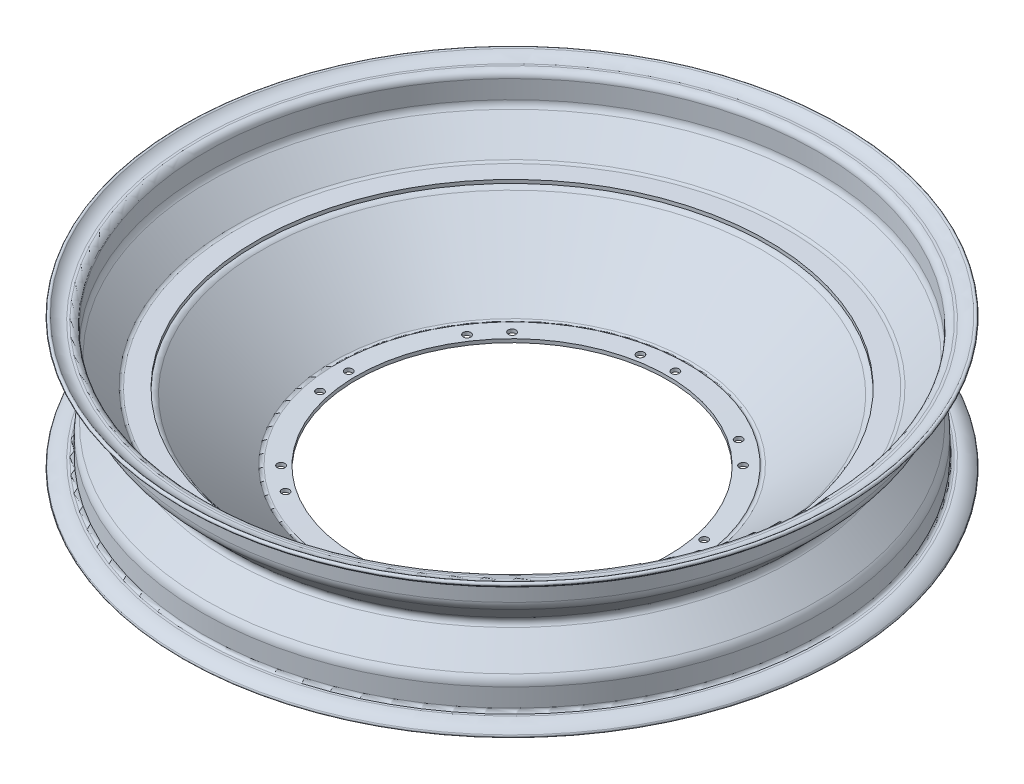
SolidWorks part; units mm, degrees
material "6061-T6 (SS)"
ref_plane "Front Plane" through (0, 0, 0) normal (0, 0, 1) x (1, 0, 0)
ref_plane "Top Plane" through (0, 0, 0) normal (0, 1, 0) x (1, 0, 0)
ref_plane "Right Plane" through (0, 0, 0) normal (1, 0, 0) x (0, 0, -1)
sketch "Sketch3" plane through (0, 0, 0) normal (0, 0, 1) x (1, 0, 0)
  line L0 (-167.2903, -3.117) -> (0, 0) construction
  line L2 (-206.3572, 37.168) -> (-204.8572, 37.168)
  line L3 (-200.5712, 32.882) -> (-200.5712, 20.882)
  line L4 (-198.7835, 16.7306) -> (-182.0435, -0.009)
  line L5 (-180.0484, -0.831) -> (-167.2903, -0.831)
  line L6 (-198.8174, -22.999) -> (-182.051, -6.2325)
  line L7 (-200.5712, -39.118) -> (-200.5712, -27.118)
  line L8 (-206.3572, -43.404) -> (-204.8572, -43.404)
  line L9 (-187.8252, -3.117) -> (-167.2903, -3.117) construction
  line L11 (-165.3527, -6.1688) -> (-118.8975, -46.2519)
  line L12 (-114.3834, -46.9352) -> (-102, -47.2925)
  line L13 (-114.3834, -46.9352) -> (-104.286, -47.2266) construction
  line L14 (-180.0484, -5.403) -> (-167.2903, -5.403)
  line L15 (-167.2903, -3.117) -> (-167.2903, 0) construction
  line L17 (-102, -45.0056) -> (-102, -48.1245) construction
  line L18 (-200.4193, -21.368) -> (-183.6674, -4.6161) construction
  line L19 (-202.8572, -39.118) -> (-202.8572, -27.118)
  line L21 (-200.4193, -21.368) -> (-184.9968, -5.9455)
  line L24 (-202.8572, 32.882) -> (-202.8572, 20.882)
  line L26 (-206.3572, 34.882) -> (-204.8572, 34.882)
  line L27 (-200.3793, 15.0935) -> (-184.9968, -0.2886)
  line L29 (-167.2903, -3.117) -> (-167.2903, -0.831)
  line L33 (-163.8292, -4.464) -> (-117.4041, -44.5211)
  line L34 (-114.9323, -44.6324) -> (-102, -45.0056)
  line L35 (-102, -45.0056) -> (-102, -47.2925)
  line L36 (-200.3793, 15.0935) -> (-183.6574, -1.628) construction
  line L39 (-206.3572, -41.118) -> (-204.8572, -41.118)
  line L41 (0, 240.889) -> (0, -99.5724) construction
  line L44 (-178.7196, -0.4999) -> (-178.7215, -5.7331) construction
  line L45 (-169.5763, -6.5618) -> (-169.5763, 0) construction
  line L46 (-104.286, -47.2266) -> (-104.286, -48.1245) construction
  line L47 (-181.0065, -3.0266) -> (-181.0066, -3.2075) construction
  arc A0 (-213.9267, 40.5243) -> (-206.3572, 37.168) centre (-206.3572, 47.382) ccw
  arc A1 (-200.5712, 32.882) -> (-204.8572, 37.168) centre (-204.8572, 32.882) ccw
  arc A2 (-200.5712, 20.882) -> (-198.7835, 16.7306) centre (-194.8572, 20.882) ccw
  arc A3 (-182.0435, -0.009) -> (-180.0484, -0.831) centre (-180.0484, 2.001) ccw
  arc A4 (-180.0484, -5.403) -> (-182.051, -6.2325) centre (-180.0484, -8.2351) ccw
  arc A6 (-198.8174, -22.999) -> (-200.5712, -27.118) centre (-194.8572, -27.118) ccw
  arc A7 (-204.8572, -43.404) -> (-200.5712, -39.118) centre (-204.8572, -39.118) ccw
  arc A8 (-206.3572, -43.404) -> (-213.9267, -46.7603) centre (-206.3572, -53.618) ccw
  arc A9 (-165.3527, -6.1688) -> (-167.2903, -5.403) centre (-167.2903, -8.2374) ccw
  arc A10 (-118.8975, -46.2519) -> (-114.3834, -46.9352) centre (-116.0975, -43.0067) ccw
  arc A11 (-182.0435, -0.009) -> (-178.7196, -0.4999) centre (-180.0484, 2.001) ccw construction
  arc A12 (-165.3527, -6.1688) -> (-169.5763, -6.5618) centre (-167.2903, -8.2374) ccw construction
  arc A13 (-178.7215, -5.7331) -> (-182.051, -6.2325) centre (-180.0484, -8.2351) ccw construction
  arc A14 (-213.9267, 40.5243) -> (-215.6209, 38.9895) centre (-214.7738, 39.7569) ccw
  arc A15 (-213.9267, -46.7603) -> (-215.6209, -45.2255) centre (-214.7738, -45.9929) cw
  arc A17 (-183.6574, -1.628) -> (-181.0065, -3.0266) centre (-180.0484, 2.001) ccw construction
  arc A18 (-204.8572, -41.118) -> (-202.8572, -39.118) centre (-204.8572, -39.118) ccw
  arc A20 (-200.4193, -21.368) -> (-202.8572, -27.118) centre (-194.8572, -27.118) ccw
  arc A22 (-202.8572, 20.882) -> (-200.3793, 15.0935) centre (-194.8572, 20.882) ccw
  arc A24 (-202.8572, 32.882) -> (-204.8572, 34.882) centre (-204.8572, 32.882) ccw
  arc A28 (-215.6209, 38.9895) -> (-206.3572, 34.882) centre (-206.3572, 47.382) ccw
  arc A31 (-181.0066, -3.2075) -> (-183.6674, -4.6161) centre (-180.0484, -8.2351) ccw construction
  arc A33 (-163.8292, -4.464) -> (-167.2903, -3.117) centre (-167.2903, -8.2374) ccw
  arc A35 (-117.4041, -44.5211) -> (-114.9323, -44.6324) centre (-116.0975, -43.0067) ccw
  arc A36 (-184.9968, -5.9455) -> (-184.9968, -0.2886) centre (-187.8252, -3.117) ccw
  arc A41 (-206.3572, -41.118) -> (-215.6209, -45.2255) centre (-206.3572, -53.618) ccw
  dimension "D1" = 41.8885
  dimension "D3" = 4
  dimension "D2" = 76
  dimension "D4" = 2.286
  dimension "D5" = 2.286
  dimension "D6" = 2.286
  dimension "D7" = 2.286
revolve "Revolve2" add sketch "Sketch3" angle 360 about L41
sketch "Sketch4" plane through (0, 0, 0) normal (0, 1, 0) x (1, 0, 0)
  line L0 (0, 0) -> (0, 107) construction
  line L1 (0, 0) -> (-20.8747, 104.944) construction
  circle A0 centre (0, 107) radius 2.5
  circle A1 centre (-3884.1816, -9484.2438) radius 2.5
  circle A2 centre (-13412.7463, -13519.7463) radius 2.5
  circle A3 centre (-23003.9901, -9635.5647) radius 2.5
  circle A4 centre (-27039.4925, -107) radius 2.5
  circle A5 centre (-23155.3109, 9484.2438) radius 2.5
  circle A6 centre (-13626.7463, 13519.7463) radius 2.5
  circle A7 centre (-4035.5024, 9635.5647) radius 2.5
  circle A8 centre (-20.8747, 104.944) radius 2.5
  circle A9 centre (-3900.396, -9470.937) radius 2.5
  circle A10 centre (-13414.8022, -13498.8716) radius 2.5
  circle A11 centre (-22990.6833, -9619.3503) radius 2.5
  circle A12 centre (-27018.6178, -104.944) radius 2.5
  circle A13 centre (-23139.0965, 9470.937) radius 2.5
  circle A14 centre (-13624.6903, 13498.8716) radius 2.5
  circle A15 centre (-4048.8092, 9619.3503) radius 2.5
  circle A16 centre (75.6604, 75.6604) radius 2.5
  circle A17 centre (59.446, 88.9672) radius 2.5
  circle A18 centre (107, 0) radius 2.5
  circle A19 centre (104.944, 20.8747) radius 2.5
  circle A20 centre (75.6604, -75.6604) radius 2.5
  circle A21 centre (88.9672, -59.446) radius 2.5
  circle A22 centre (0, -107) radius 2.5
  circle A23 centre (20.8747, -104.944) radius 2.5
  circle A24 centre (-75.6604, -75.6604) radius 2.5
  circle A25 centre (-59.446, -88.9672) radius 2.5
  circle A26 centre (-107, 0) radius 2.5
  circle A27 centre (-104.944, -20.8747) radius 2.5
  circle A28 centre (-75.6604, 75.6604) radius 2.5
  circle A29 centre (-88.9672, 59.446) radius 2.5
  point P19 (-13519.7463, 0)
  point P37 (-13519.7463, 0)
  point P67 (0, 0)
  dimension "D1" = 107
  dimension "D2" = 5
  dimension "D4" = 11.25
  dimension "D5" = 8
  dimension "D3" = 8
  dimension "D6" = 8
extrude "Cut-Extrude3" cut sketch "Sketch4" against normal through all both and the other way through all
